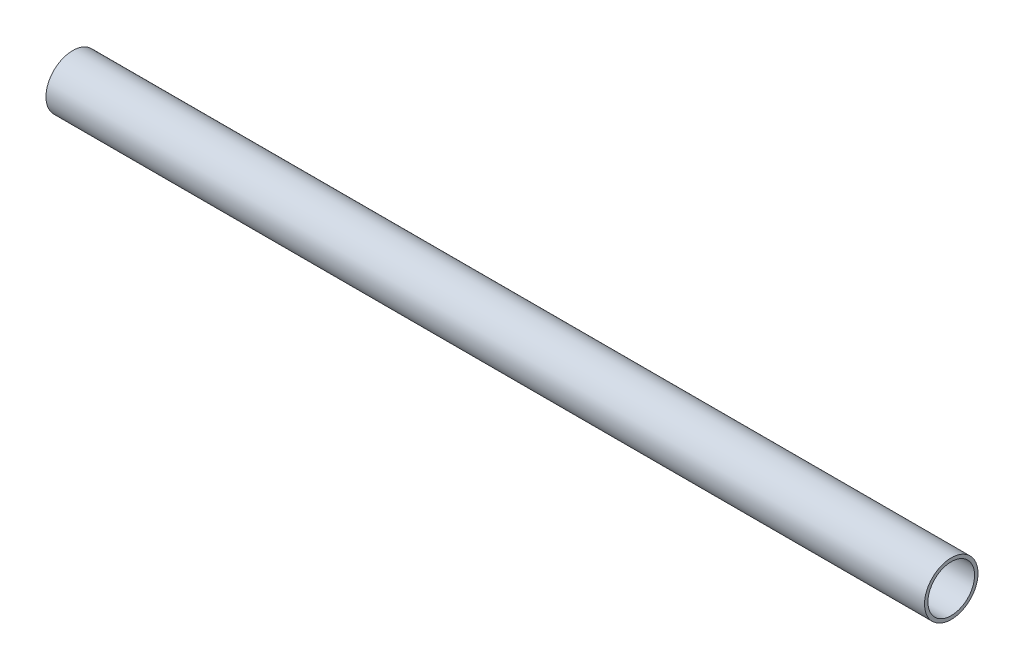
SolidWorks part; units mm, degrees
ref_plane "Front" through (0, 0, 0) normal (0, 0, 1) x (1, 0, 0)
ref_plane "Top" through (0, 0, 0) normal (0, 1, 0) x (1, 0, 0)
ref_plane "Right" through (0, 0, 0) normal (1, 0, 0) x (0, 0, -1)
sketch "Sketch1" plane through (0, 0, 0) normal (1, 0, 0) x (0, 0, -1)
  circle A0 centre (0, 0) radius 6.35
  circle A1 centre (0, 0) radius 5.5372
  point P4 (6.35, 0)
  point P5 (5.5372, 0)
  dimension "OD" = 12.7
  dimension "ID" = 11.0744
  dimension "Wall" = 0.8128
extrude "Extrude1" add sketch "Sketch1" along normal blind 208.5721
